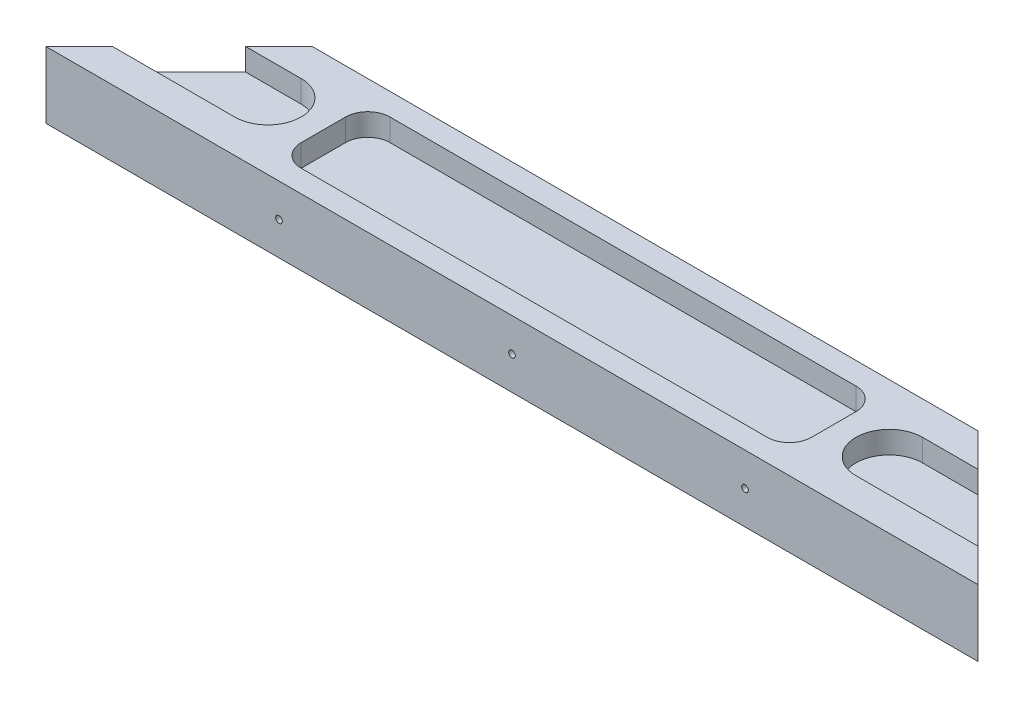
SolidWorks part; units mm, degrees
ref_plane "Front Plane" through (0, 0, 0) normal (0, 0, 1) x (1, 0, 0)
ref_plane "Top Plane" through (0, 0, 0) normal (0, 1, 0) x (1, 0, 0)
ref_plane "Right Plane" through (0, 0, 0) normal (1, 0, 0) x (0, 0, -1)
sketch "Sketch1" plane through (0, 0, 0) normal (0, 1, 0) x (1, 0, 0)
  line L0 (0, 0) -> (210, 0)
  line L1 (210, 0) -> (180, 30)
  line L2 (180, 30) -> (30, 30)
  line L3 (30, 30) -> (0, 0)
  point P3 (105, 30)
  point P6 (105, 0)
  dimension "D1" = 210
  dimension "D2" = 150
  dimension "D3" = 30
extrude "Boss-Extrude1" add sketch "Sketch1" along normal blind 15
sketch "Sketch2" plane through (0, 15, 0) normal (0, 1, 0) x (1, 0, 0)
  line L0 (-5, 15) -> (35, 15) construction
  line L1 (-5, 22.5) -> (35, 22.5)
  line L2 (-5, 7.5) -> (35, 7.5)
  line L3 (30, 30) -> (0, 0) construction
  line L4 (105, 30) -> (105, 0) construction
  line L5 (180, 30) -> (30, 30) construction
  line L6 (0, 0) -> (210, 0) construction
  line L7 (215, 15) -> (175, 15) construction
  line L8 (215, 22.5) -> (175, 22.5)
  line L9 (215, 7.5) -> (175, 7.5)
  arc A0 (-5, 22.5) -> (-5, 7.5) centre (-5, 15) ccw
  arc A1 (35, 7.5) -> (35, 22.5) centre (35, 15) ccw
  arc A2 (215, 22.5) -> (215, 7.5) centre (215, 15) cw
  arc A3 (175, 7.5) -> (175, 22.5) centre (175, 15) cw
  point P2 (15, 15)
  point P9 (15, 15)
  point P18 (195, 15)
  dimension "D1" = 40
  dimension "D2" = 15
extrude "Cut-Extrude1" cut sketch "Sketch2" against normal blind 5
sketch "Sketch3" plane through (0, 0, 0) normal (0, 0, 1) x (1, 0, 0)
  line L0 (0, 7.5) -> (210, 7.5) construction
  line L1 (0, 15) -> (0, 0) construction
  line L2 (210, 15) -> (210, 0) construction
  circle A0 centre (105, 7.5) radius 0.75
  circle A1 centre (52.5, 7.5) radius 0.75
  circle A2 centre (157.5, 7.5) radius 0.75
  dimension "D1" = 1.5
  dimension "D2" = 52.5
  dimension "D3" = 52.5
extrude "Cut-Extrude2" cut sketch "Sketch3" against normal up to surface (30 mm away) up to face at (105, 7.5, -30)
sketch "Sketch4" plane through (0, 15, 0) normal (0, 1, 0) x (1, 0, 0)
  line L0 (180, 30) -> (30, 30) construction
  line L1 (52.5, 25) -> (157.5, 25)
  line L2 (47.5, 20) -> (47.5, 10)
  line L3 (52.5, 5) -> (157.5, 5)
  line L4 (162.5, 20) -> (162.5, 10)
  line L5 (0, 0) -> (210, 0) construction
  arc A0 (35, 7.5) -> (35, 22.5) centre (35, 15) ccw construction
  arc A1 (175, 22.5) -> (175, 7.5) centre (175, 15) ccw construction
  arc A2 (157.5, 25) -> (162.5, 20) centre (157.5, 20) cw
  arc A3 (157.5, 5) -> (162.5, 10) centre (157.5, 10) ccw
  arc A4 (47.5, 10) -> (52.5, 5) centre (52.5, 10) ccw
  arc A5 (52.5, 25) -> (47.5, 20) centre (52.5, 20) ccw
  point P4 (42.5, 15)
  point P5 (167.5, 15)
  dimension "D5" = 5
  dimension "D1" = 5
  dimension "D2" = 5
  dimension "D3" = 5
  dimension "D4" = 5
extrude "Cut-Extrude3" cut sketch "Sketch4" against normal blind 5
